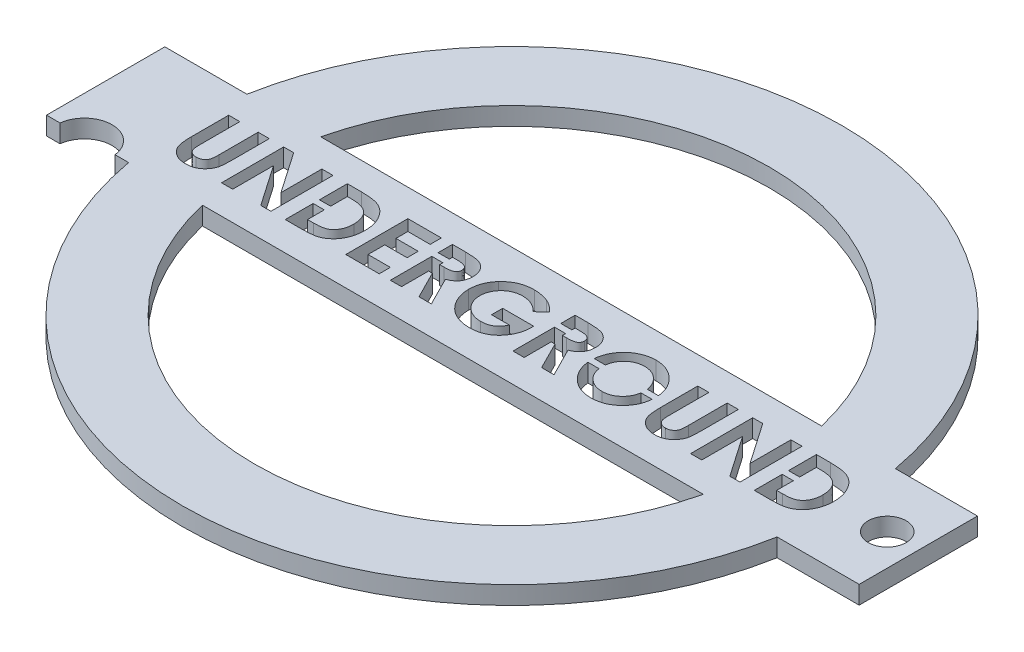
SolidWorks part; units mm, degrees
ref_plane "Frontal Plane" through (0, 0, 0) normal (0, 0, 1) x (1, 0, 0)
ref_plane "Top Plane" through (0, 0, 0) normal (0, 1, 0) x (1, 0, 0)
ref_plane "Right Plane" through (0, 0, 0) normal (1, 0, 0) x (0, 0, -1)
sketch "Sketch1" plane through (0, 0, 0) normal (0, 1, 0) x (1, 0, 0)
  line L0 (4.5447, 26.5878) -> (13.6377, 26.588)
  line L1 (-16.8623, -346.8595) -> (16.1377, -346.8595) construction
  line L2 (-16.8623, -346.8595) -> (-16.8623, 413.1405) construction
  line L3 (-16.8623, 413.1405) -> (16.1377, 413.1405) construction
  line L4 (16.1377, -346.8595) -> (16.1377, 413.1405) construction
  line L5 (4.5447, 39.693) -> (13.6377, 39.693)
  line L7 (-78.8623, -346.8595) -> (-46.8623, -346.8595) construction
  line L8 (-78.8623, -346.8595) -> (-78.8623, 413.1405) construction
  line L9 (-78.8623, 413.1405) -> (-46.8623, 413.1405) construction
  line L10 (-46.8623, -346.8595) -> (-46.8623, 413.1405) construction
  line L11 (-76.3623, 26.588) -> (-76.3623, 39.693)
  line L12 (-76.3623, 39.693) -> (-67.2693, 39.693)
  line L13 (13.6377, 26.588) -> (13.6377, 39.693)
  line L14 (-76.3623, 26.588) -> (13.6377, 39.693) construction
  line L15 (-76.3623, 39.693) -> (13.6377, 26.588) construction
  line L16 (-59.0988, 39.693) -> (-3.6258, 39.693)
  line L17 (-59.0988, 26.588) -> (-3.6258, 26.588)
  line L18 (-76.3623, 26.588) -> (-74.8623, 26.588)
  line L19 (-67.2693, 26.588) -> (-68.7693, 26.588)
  arc A2 (-67.2693, 26.588) -> (4.5447, 26.5878) centre (-31.3623, 33.1405) ccw
  arc A3 (-59.0988, 26.588) -> (-3.6258, 26.588) centre (-31.3623, 33.1405) ccw
  arc A4 (-3.6258, 39.693) -> (-59.0988, 39.693) centre (-31.3623, 33.1405) ccw
  arc A5 (4.5447, 39.693) -> (-67.2693, 39.693) centre (-31.3623, 33.1405) ccw
  arc A8 (-74.8623, 26.588) -> (-68.7693, 26.588) centre (-71.8158, 26.2374) cw
  point P16 (-46.8623, 33.1405)
  point P17 (-16.8623, 33.1405)
  dimension "D5" = 5
  dimension "D6" = 47.5
  dimension "D8" = 73
  dimension "D9" = 57
  dimension "D11" = 13.105
  dimension "D1" = 760
  dimension "D2" = 33
  dimension "D3" = 32
  dimension "D4" = 95
  dimension "D7" = 5
  dimension "D10" = 1.5
extrude "Boss-Extrude1" add sketch "Sketch1" along normal blind 2
sketch "Sketch2" plane through (0, 2, 0) normal (0, 1, 0) x (1, 0, 0)
  line L1 (-76.3623, 39.693) -> (-76.3623, 26.588) construction
  line L2 (-67.2693, 39.693) -> (-76.3623, 39.693) construction
  text T0 "UNDERGROUND" font "Century Gothic" height in points 26
  dimension "D1" = 9.9
  dimension "D2" = 9.3
extrude "Cut-Extrude1" cut sketch "Sketch2" against normal blind 2
sketch "Sketch3" plane through (0, 2, 0) normal (0, 1, 0) x (1, 0, 0)
  line L0 (13.6377, 26.588) -> (13.6377, 39.693) construction
  line L1 (13.6377, 39.693) -> (4.5447, 39.693) construction
  circle A0 centre (10.1377, 33.193) radius 2.1
  dimension "D1" = 4.2
  dimension "D2" = 3.5
  dimension "D3" = 6.5
extrude "Cut-Extrude2" cut sketch "Sketch3" against normal blind 2
sketch "Sketch6" plane through (0, 2, 0) normal (0, 1, 0) x (1, 0, 0)
  line L0 (-51.8929, 35.4375) -> (-51.8929, 31.0277) construction
  line L1 (-51.8929, 33.5826) -> (-53.1276, 33.5826)
  line L2 (-51.8929, 33.5826) -> (-51.8929, 32.8826)
  line L3 (-51.8929, 32.8826) -> (-53.1276, 32.8826)
  line L4 (-53.1276, 33.5826) -> (-53.1276, 32.8826)
  line L5 (-53.1276, 29.793) -> (-53.1276, 36.6722) construction
  line L6 (-40.2512, 35.4375) -> (-40.2512, 34.0263) construction
  line L7 (-40.2512, 34.3819) -> (-41.4859, 34.3819)
  line L8 (-40.2512, 34.3819) -> (-40.2512, 35.0819)
  line L9 (-40.2512, 35.0819) -> (-41.4859, 35.0819)
  line L10 (-41.4859, 34.3819) -> (-41.4859, 35.0819)
  line L11 (-41.4859, 29.793) -> (-41.4859, 36.6722) construction
  line L12 (-27.904, 29.793) -> (-27.904, 36.6722) construction
  line L13 (-27.904, 35.0847) -> (-26.6693, 35.0847)
  line L14 (-27.904, 35.0847) -> (-27.904, 34.3847)
  line L15 (-27.904, 34.3847) -> (-26.6693, 34.3847)
  line L16 (-26.6693, 35.0847) -> (-26.6693, 34.3847)
  line L17 (-26.6693, 35.4375) -> (-26.6693, 34.0263) construction
  line L18 (0.0537, 35.4375) -> (0.0537, 31.0277) construction
  line L19 (0.0537, 32.8826) -> (-1.1811, 32.8826)
  line L20 (0.0537, 32.8826) -> (0.0537, 33.5826)
  line L21 (0.0537, 33.5826) -> (-1.1811, 33.5826)
  line L22 (-1.1811, 32.8826) -> (-1.1811, 33.5826)
  line L23 (-1.1811, 29.793) -> (-1.1811, 36.6722) construction
  line L24 (-21.4452, 33.5688) -> (-22.6869, 33.5688)
  line L25 (-21.4452, 32.8688) -> (-22.6836, 32.8688)
  line L26 (-16.8123, 33.5688) -> (-15.5719, 33.5688)
  line L27 (-16.8148, 32.8688) -> (-15.5712, 32.8688)
  spline S0 degree 3 poles (-209.6726, 3029.4689) (-2.7767, 1.5836) (-12.4254, 36.5757) (-19.6065, 35.5749) (-19.8302, 35.5231) (-20.0434, 35.448) (-20.2469, 35.3523) (-20.4412, 35.2366) (-20.6235, 35.0966) (-20.7962, 34.9401) (-20.9523, 34.7657) (-21.0902, 34.5788) (-21.2056, 34.3797) (-21.3022, 34.1702) (-21.375, 33.9481) (-21.4268, 33.715) (-22.4331, 26.2033) (12.9741, 16.3349) (-3016.0727, 211.5959) knots -5.621244 -5.621244 -5.621244 -5.621244 0.064609 0.127512 0.188521 0.248708 0.308598 0.368812 0.429888 0.492802 0.555743 0.617485 0.678969 0.740198 0.80236 0.866245 0.931707 6.875611 6.875611 6.875611 6.875611 only from (-19.1341, 35.6138) to (-21.4658, 33.2188) construction
  spline S1 degree 3 poles (-3019.5251, 169.0486) (9.3762, 16.4984) (-23.4855, 25.9592) (-22.6723, 33.7181) (-22.6361, 33.953) (-22.5826, 34.1824) (-22.5176, 34.4078) (-22.4335, 34.627) (-22.3377, 34.8425) (-22.2257, 35.0517) (-22.1012, 35.2527) (-21.9654, 35.4446) (-21.8179, 35.6249) (-21.6592, 35.7949) (-21.4888, 35.9535) (-21.3088, 36.103) (-21.1159, 36.2392) (-20.9142, 36.3657) (-20.7048, 36.4801) (-20.4886, 36.5774) (-20.2701, 36.6624) (-20.0464, 36.7295) (-19.8198, 36.7841) (-19.5879, 36.8203) (-11.9843, 37.6328) (-2.6368, 4.8664) (-159.4577, 3033.4792) knots -4.003459 -4.003459 -4.003459 -4.003459 0.043114 0.085683 0.127594 0.169059 0.210432 0.251811 0.293444 0.335381 0.377477 0.418688 0.459873 0.500873 0.541873 0.583212 0.624763 0.666988 0.70937 0.751103 0.792568 0.833545 0.874827 0.916018 0.957859 4.923994 4.923994 4.923994 4.923994 only from (-22.7005, 33.2353) to (-19.1148, 36.8486) construction
  spline S2 degree 3 poles (-3015.5052, -153.411) (14.511, 51.173) (-22.5562, 40.6258) (-21.419, 32.6701) (-21.3531, 32.4156) (-21.2579, 32.1772) (-21.1398, 31.9524) (-20.9932, 31.744) (-16.1784, 26.3572) (16.159, 50.2731) (-2063.721, -2165.1072) knots -11.075749 -11.075749 -11.075749 -11.075749 0.134807 0.264199 0.388462 0.509942 0.63041 0.750671 0.873455 10.928189 10.928189 10.928189 10.928189 only from (-21.4658, 33.2188) to (-20.6197, 31.3805) construction
  spline S3 degree 3 poles (-216.154, -2963.697) (2.1572, 70.6263) (-10.4238, 28.2915) (-19.8441, 29.6787) (-20.1927, 29.7594) (-20.5231, 29.8798) (-20.8387, 30.0304) (-21.1371, 30.2158) (-21.4183, 30.4358) (-21.6807, 30.6847) (-21.9184, 30.9571) (-22.1282, 31.2448) (-22.3052, 31.5457) (-22.4494, 31.8599) (-22.563, 32.1854) (-22.6432, 32.5243) (-23.9401, 42.1472) (15.5712, 54.3649) (-3017.5797, -137.6072) knots -4.822617 -4.822617 -4.822617 -4.822617 0.066749 0.131152 0.193732 0.255326 0.316388 0.378027 0.440406 0.504557 0.568658 0.630986 0.692288 0.752615 0.8132 0.874016 0.936158 5.928485 5.928485 5.928485 5.928485 only from (-19.1052, 29.6166) to (-22.7005, 33.2353) construction
  spline S4 degree 3 poles (-22.7005, 33.2353) (-22.6995, 33.3167) (-22.698, 33.428) (-22.6896, 33.539) (-22.6869, 33.5688) knots 0 0 0 0 0.043114 0.058984 0.058984 0.058984 0.058984
  spline S5 degree 3 poles (-22.6836, 32.8688) (-22.6837, 32.8702) (-22.6938, 32.9921) (-22.6972, 33.1144) (-22.7005, 33.2353) knots 0.935432 0.935432 0.935432 0.935432 0.936158 1 1 1 1
  spline S6 degree 3 poles (-21.4658, 33.2188) (-21.463, 33.1245) (-21.4595, 33.0076) (-21.4478, 32.8913) (-21.4452, 32.8688) knots 0 0 0 0 0.134807 0.167141 0.167141 0.167141 0.167141
  spline S7 degree 3 poles (-21.4452, 33.5688) (-21.449, 33.5372) (-21.4608, 33.4208) (-21.4637, 33.3039) (-21.4658, 33.2188) knots 0.906137 0.906137 0.906137 0.906137 0.931707 1 1 1 1
  spline S8 degree 3 poles (2977.9343, 209.4003) (-50.699, 16.7493) (-15.8351, 26.3734) (-16.8301, 33.7083) (-16.884, 33.9353) (-16.9587, 34.1527) (-17.0541, 34.3609) (-17.172, 34.5589) (-17.3121, 34.7467) (-17.4711, 34.923) (-17.6442, 35.085) (-17.8301, 35.2256) (-18.0234, 35.3477) (-18.2288, 35.4434) (-18.4419, 35.5197) (-18.6641, 35.5758) (-25.9335, 36.5591) (-35.3461, 2.1854) (147.5663, 3030.7987) knots -5.758474 -5.758474 -5.758474 -5.758474 0.065939 0.129791 0.192175 0.253617 0.314719 0.376282 0.438973 0.503175 0.567329 0.629651 0.69065 0.751238 0.811754 0.872788 0.93554 6.707266 6.707266 6.707266 6.707266 only from (-16.7915, 33.2285) to (-19.1341, 35.6138) construction
  spline S9 degree 3 poles (168.2648, 3030.8714) (-39.685, -2.8854) (-27.5904, 38.1354) (-18.4119, 36.7884) (-18.0772, 36.7054) (-17.7554, 36.5899) (-17.447, 36.439) (-17.1512, 36.2568) (-16.8689, 36.04) (-16.6031, 35.7935) (-16.3574, 35.5255) (-16.1445, 35.2369) (-15.9629, 34.9352) (-15.8124, 34.6197) (-15.6978, 34.2881) (-15.6174, 33.9421) (-14.259, 24.4712) (-55.7254, 12.0477) (2978.4198, 220.2814) knots -4.721418 -4.721418 -4.721418 -4.721418 0.063396 0.125157 0.185649 0.245977 0.306108 0.367351 0.429902 0.49454 0.559373 0.62241 0.684357 0.745807 0.80743 0.869996 0.933928 5.869978 5.869978 5.869978 5.869978 only from (-19.1148, 36.8486) to (-15.5568, 33.2119) construction
  spline S10 degree 3 poles (162.2558, -2963.4696) (-35.1658, 64.7412) (-25.7336, 29.8957) (-18.6459, 30.8899) (-18.4268, 30.9442) (-18.216, 31.0186) (-18.014, 31.1155) (-17.8218, 31.2348) (-17.6391, 31.3753) (-17.4666, 31.5339) (-17.3089, 31.709) (-17.1713, 31.8969) (-17.0522, 32.0935) (-16.9576, 32.3015) (-16.8819, 32.519) (-16.8307, 32.747) (-15.8216, 40.0041) (-51.2552, 49.8043) (2976.8012, -160.8114) knots -5.604067 -5.604067 -5.604067 -5.604067 0.064147 0.126212 0.186841 0.246936 0.307256 0.368151 0.430071 0.493875 0.557981 0.62087 0.682525 0.744036 0.805889 0.868968 0.933247 6.737374 6.737374 6.737374 6.737374 only from (-19.1093, 30.8513) to (-16.7915, 33.2285) construction
  spline S11 degree 3 poles (2979.4588, -137.1224) (-54.597, 54.3822) (-14.2946, 42.1154) (-15.6153, 32.4888) (-15.6971, 32.1466) (-15.8097, 31.8182) (-15.9575, 31.5053) (-16.1355, 31.2059) (-16.3485, 30.9227) (-16.5886, 30.656) (-16.8531, 30.4138) (-17.1331, 30.2005) (-17.4275, 30.0197) (-17.7359, 29.8715) (-18.0588, 29.7565) (-18.3955, 29.6754) (-27.811, 28.3508) (-40.0046, 68.7725) (160.9509, -2964.7855) knots -4.978987 -4.978987 -4.978987 -4.978987 0.065722 0.129508 0.191722 0.253161 0.314316 0.375952 0.43862 0.502973 0.567129 0.629552 0.690477 0.751072 0.811668 0.872929 0.935501 5.871595 5.871595 5.871595 5.871595 only from (-15.5568, 33.2119) to (-19.1052, 29.6166) construction
  spline S12 degree 3 poles (-15.5568, 33.2119) (-15.5597, 33.0974) (-15.5627, 32.9829) (-15.5712, 32.8688) knots 0 0 0 0 0.061049 0.061049 0.061049 0.061049
  spline S13 degree 3 poles (-15.5719, 33.5688) (-15.5625, 33.4502) (-15.5596, 33.331) (-15.5568, 33.2119) knots 0.936865 0.936865 0.936865 0.936865 1 1 1 1
  spline S14 degree 3 poles (-16.7915, 33.2285) (-16.7937, 33.3103) (-16.7967, 33.424) (-16.8084, 33.5372) (-16.8123, 33.5688) knots 0 0 0 0 0.065939 0.091601 0.091601 0.091601 0.091601
  spline S15 degree 3 poles (-16.8148, 32.8688) (-16.8098, 32.9064) (-16.7967, 33.0259) (-16.7936, 33.1461) (-16.7915, 33.2285) knots 0.902523 0.902523 0.902523 0.902523 0.933247 1 1 1 1
  point P8 (-51.8929, 33.2326)
  point P9 (-51.8929, 33.2326)
  point P18 (-40.2512, 34.7319)
  point P19 (-40.2512, 34.7319)
  point P28 (-26.6693, 34.7347)
  point P38 (0.0537, 33.2326)
  point P39 (0.0537, 33.2326)
  dimension "D1" = 0.7
  dimension "D2" = 0.7
  dimension "D3" = 0.7
  dimension "D4" = 0.7
  dimension "D5" = 0.7
  dimension "D6" = 0.35
extrude "Boss-Extrude3" add sketch "Sketch6" against normal up to surface (2 mm away) up to face at (10.1377, 0, -31.093)
